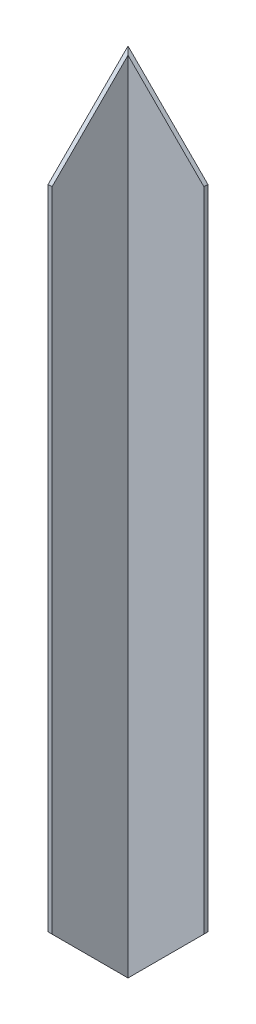
SolidWorks part; units mm, degrees
ref_plane "Plan de face" through (0, 0, 0) normal (0, 0, 1) x (1, 0, 0)
ref_plane "Plan de dessus" through (0, 0, 0) normal (0, 1, 0) x (1, 0, 0)
ref_plane "Plan de droite" through (0, 0, 0) normal (1, 0, 0) x (0, 0, -1)
sketch "Esquisse1" plane through (0, 0, 0) normal (0, 1, 0) x (1, 0, 0)
  line L1 (-20, 20.1136) -> (20, 20.1136)
  line L2 (-20, 20.1136) -> (-20, -19.8864)
  line L3 (-20, -19.8864) -> (-18, -19.8864)
  line L4 (20, 20.1136) -> (20, 18.1136)
  line L5 (-18, 18.1136) -> (20, 18.1136)
  line L6 (-18, 18.1136) -> (-18, -19.8864)
  dimension "D1" = 20
  dimension "D2" = 40
  dimension "D3" = 40
  dimension "D4" = 2
  dimension "D5" = 2
extrude "Boss.-Extru.1" add sketch "Esquisse1" along normal blind 404
sketch "Esquisse2" plane through (0, 0, -20.1136) normal (0, 0, -1) x (-1, 0, 0)
  line L0 (20, 0) -> (-20, 40)
  line L1 (20, 0) -> (-20, 0)
  line L2 (-20, 0) -> (-20, 40)
  dimension "D1" = 45
extrude "Enlèv. mat.-Extru.1" cut sketch "Esquisse2" against normal blind 590
sketch "Esquisse3" plane through (-20, 0, 0) normal (-1, 0, 0) x (0, 0, 1)
  line L0 (-20.1136, 0) -> (19.8864, 40)
  line L1 (19.8864, 404) -> (19.8864, 0) construction
  line L2 (19.8864, 40) -> (19.8864, 0)
  line L3 (19.8864, 0) -> (-20.1136, 0)
  dimension "D1" = 45
extrude "Enlèv. mat.-Extru.2" cut sketch "Esquisse3" against normal blind 590
sketch "Esquisse4" plane through (-20, 0, 0) normal (-1, 0, 0) x (0, 0, 1)
  line L0 (-20.1136, 404) -> (19.8864, 364)
  line L1 (19.8864, 404) -> (19.8864, 40) construction
  line L2 (19.8864, 364) -> (19.8864, 404)
  line L3 (19.8864, 404) -> (-20.1136, 404)
  dimension "D1" = 45
extrude "Enlèv. mat.-Extru.3" cut sketch "Esquisse4" against normal through all
sketch "Esquisse5" plane through (0, 0, -20.1136) normal (0, 0, -1) x (-1, 0, 0)
  line L0 (20, 404) -> (-20, 364)
  line L1 (-20, 404) -> (-20, 40) construction
  line L2 (-20, 364) -> (-20, 404)
  line L3 (-20, 404) -> (20, 404)
  dimension "D1" = 45
extrude "Enlèv. mat.-Extru.4" cut sketch "Esquisse5" against normal through all
